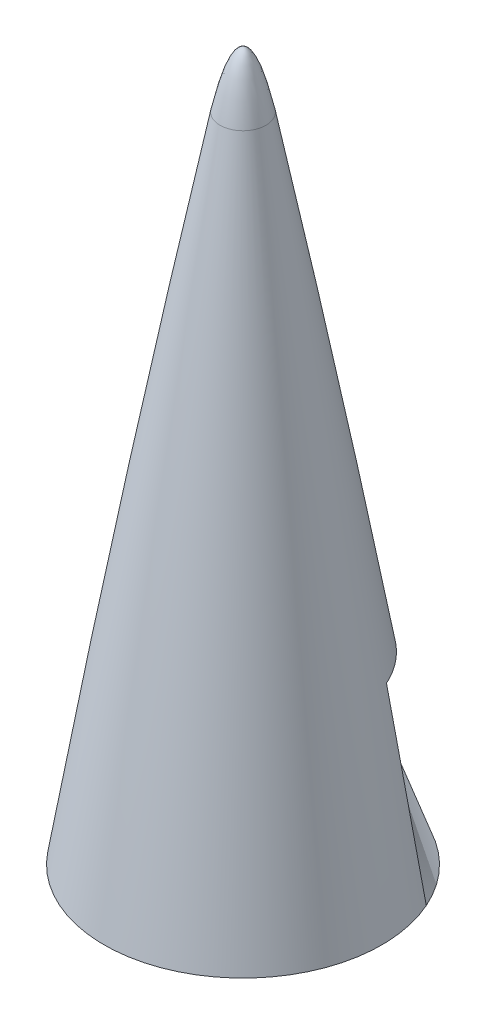
SolidWorks part; units mm, degrees
material "6061-T6 (SS)"
ref_plane "Front Plane" through (0, 0, 0) normal (0, 0, 1) x (1, 0, 0)
ref_plane "Top Plane" through (0, 0, 0) normal (0, 1, 0) x (1, 0, 0)
ref_plane "Right Plane" through (0, 0, 0) normal (1, 0, 0) x (0, 0, -1)
sketch "Sketch1" plane through (0, 0, 0) normal (0, 0, 1) x (1, 0, 0)
  line L1 (0, 0) -> (0, 812.8) construction
  line L2 (-101.6, 0) -> (0, 0) construction
  line L3 (0, 812.8) -> (-36.8107, 812.8)
  line L4 (0, 1016) -> (0, 812.8)
  arc A0 (0, 1016) -> (-36.8107, 812.8) centre (5029.2, 0) ccw
  spline S0 degree 4 poles (-23.2398, 893.2866) (-23.5393, 891.5924) (-24.137, 888.2033) (-25.0296, 883.1148) (-26.2088, 876.3394) (-27.3767, 869.5744) (-28.525, 862.8715) (-29.6693, 856.1347) (-30.7805, 849.5464) (-31.9198, 842.7267) (-32.9792, 836.3481) (-34.1672, 829.1125) (-35.0792, 823.5406) (-36.435, 815.1441) (-37.0457, 811.3406) (-38.406, 802.8129) (-39.4063, 796.4669) (-40.5094, 789.4175) (-41.5637, 782.6088) (-42.4113, 777.0973) (-43.2542, 771.5761) (-44.0966, 766.0177) (-44.9373, 760.4296) (-45.7763, 754.8098) (-46.8172, 747.7841) (-48.054, 739.3514) (-49.4786, 729.5106) (-51.8836, 712.6352) (-56.1784, 681.6809) (-64.3109, 619.7097) (-79.957, 484.2341) (-91.5619, 342.6137) (-98.2797, 206.3794) (-100.6652, 101.2886) (-101.1219, 71.4617) (-101.3057, 55.1272) (-101.3623, 49.4455) (-101.4013, 45.2149) (-101.437, 41.0149) (-101.474, 36.1352) (-101.5101, 30.575) (-101.5403, 25.0243) (-101.5644, 19.4326) (-101.5824, 13.9273) (-101.5945, 8.4855) (-101.6008, 1.478) (-101.6004, -2.3538) (-101.5919, -10.831) (-101.5742, -16.4582) (-101.5477, -23.7538) (-101.5124, -30.1968) (-101.4682, -37.0784) (-101.4152, -43.7331) (-101.3531, -50.5363) (-101.2817, -57.3091) (-101.201, -64.1452) (-101.1107, -70.9945) (-101.0361, -76.1392) (-100.9833, -79.5663) (-100.9562, -81.2797) knots 0 0 0 0 0 0.007031 0.014061 0.021092 0.028122 0.035027 0.041932 0.048837 0.055742 0.062647 0.069552 0.076457 0.083362 0.08904 0.094718 0.106073 0.111751 0.117429 0.123106 0.128784 0.134587 0.14039 0.146193 0.151996 0.163602 0.175208 0.186814 0.221632 0.291267 0.430538 0.743898 0.801928 0.848352 0.859958 0.865761 0.868662 0.871564 0.877241 0.882919 0.888597 0.894275 0.899952 0.90563 0.911308 0.916985 0.923861 0.930737 0.937613 0.944488 0.951364 0.95824 0.965115 0.971991 0.978993 0.985996 0.992998 1 1 1 1 1 construction
  spline S1 degree 4 poles (-36.8107, 812.8) (-36.9943, 811.656) (-37.3629, 809.3523) (-38.406, 802.8129) (-39.4063, 796.4669) (-40.5094, 789.4175) (-41.5637, 782.6088) (-42.4113, 777.0973) (-43.2542, 771.5761) (-44.0966, 766.0177) (-44.9373, 760.4296) (-45.7763, 754.8098) (-46.8172, 747.7841) (-48.054, 739.3514) (-49.4786, 729.5106) (-51.8836, 712.6352) (-56.1784, 681.6809) (-64.3109, 619.7097) (-79.957, 484.2341) (-91.5619, 342.6137) (-98.2797, 206.3794) (-100.6652, 101.2886) (-101.1219, 71.4617) (-101.3057, 55.1272) (-101.3623, 49.4455) (-101.4013, 45.2149) (-101.437, 41.0149) (-101.474, 36.1352) (-101.5101, 30.575) (-101.5403, 25.0243) (-101.5644, 19.4326) (-101.5824, 13.9273) (-101.5945, 8.4855) (-101.599, 3.4932) (-101.6, 1.1586) (-101.6, 0) knots 0.083362 0.083362 0.083362 0.083362 0.083362 0.08904 0.094718 0.106073 0.111751 0.117429 0.123106 0.128784 0.134587 0.14039 0.146193 0.151996 0.163602 0.175208 0.186814 0.221632 0.291267 0.430538 0.743898 0.801928 0.848352 0.859958 0.865761 0.868662 0.871564 0.877241 0.882919 0.888597 0.894275 0.899952 0.90563 0.911308 0.916985 0.916985 0.916985 0.916985 0.916985 construction
  point P7 (0, 1016)
  dimension "D2" = 1016
  dimension "D1" = 203.2
revolve "Revolve1" add sketch "Sketch1" angle 360 about L4
sketch "Sketch2" plane through (0, 0, 0) normal (1, 0, 0) x (0, 0, -1)
  line L0 (0, 985.4578) -> (0, 1000.3225) construction
  line L2 (8.1031, 1019.1786) -> (8.7378, 985.4578)
  line L3 (8.7378, 985.4578) -> (6.0737, 985.4578)
  line L4 (0, 1000.3225) -> (0, 1019.1786)
  line L5 (0, 1019.1786) -> (8.1031, 1019.1786)
  arc A0 (36.8107, 812.8) -> (0, 1016) centre (-5029.2, 0) ccw construction
  spline S0 degree 2 poles (6.0737, 985.4578) (3.0132, 1000.3387) (0, 1000.3225) knots 0 0 0 0.500461 0.500461 0.500461
revolve "Cut-Revolve1" cut sketch "Sketch2" angle 360 about L0
equation "\"R\"= 4in"
equation "\"L\"= 40in"
equation "\"D2@Sketch1\" = \"L\""
equation "\"p\"= ( \"R\" ^ 2 + \"L\" ^ 2 ) / ( \"R\" * 2 )"
equation "\"tip_Length\"= ( \"R\" * 2 )"
equation "\"D1@Sketch1\"=\"tip_Length\""
